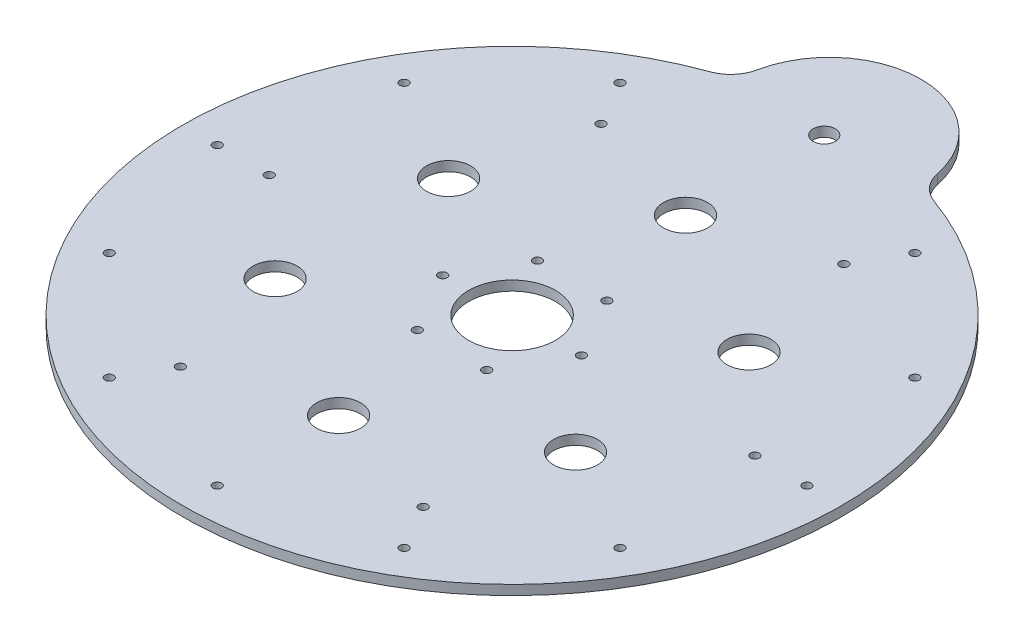
SolidWorks part; units mm, degrees
ref_plane "Front Plane" through (0, 0, 0) normal (0, 0, 1) x (1, 0, 0)
ref_plane "Top Plane" through (0, 0, 0) normal (0, 1, 0) x (1, 0, 0)
ref_plane "Right Plane" through (0, 0, 0) normal (1, 0, 0) x (0, 0, -1)
sketch "Sketch1" plane through (0, 0, 0) normal (0, -1, 0) x (1, 0, 0)
  line L0 (0, 0) -> (0, -337.6782) construction
  arc A0 (-51.8173, -193.4909) -> (51.8173, -193.4909) centre (0, -182.9328) ccw
  circle A1 centre (0, 0) radius 25
  circle A2 centre (0, 100) radius 12.7
  arc A3 (-51.8173, -193.4909) -> (-64.6132, -178.676) centre (-71.4146, -197.484) ccw
  arc A4 (51.8173, -193.4909) -> (64.6132, -178.676) centre (71.4146, -197.484) cw
  arc A5 (64.6132, -178.676) -> (-64.6132, -178.676) centre (0, 0) ccw
  circle A9 centre (-0.0097, -180) radius 6.35
  point P0 (0, 0)
  dimension "D1" = 20
  dimension "D2" = 50
  dimension "D3" = 20
extrude "Boss-Extrude1" add sketch "Sketch1" along normal blind 5.6
hole_wizard "Ø5.0mm Dowel Hole2" positions "Sketch7" profile "Sketch6" hole size "Ø5.0" standard "ANSI Metric" end condition through all
sketch "Sketch7" plane through (0, 0, 0) normal (0, -1, 0) x (1, 0, 0)
  point P0 (-147.2243, -85)
sketch "Sketch6" plane through (-147.2243, 0, -85) normal (1, 0, 0) x (0, 0, 1)
  line L0 (0, 0) -> (0, 5.6)
  line L1 (0, 5.6) -> (2.5, 5.6)
  line L2 (2.5, 5.6) -> (2.5, 0)
  line L5 (2.5, 0) -> (0, 0)
  line L11 (0, -6.35) -> (0, 107.95) construction
  dimension "Thru Hole Dia." = 5
  dimension "Thru Hole Depth" = 5.6
hole_wizard "Ø5.0mm Dowel Hole3" positions "Sketch9" profile "Sketch8" hole size "Ø5.0" standard "ANSI Metric" end condition through all
sketch "Sketch9" plane through (0, 0, 0) normal (0, 1, 0) x (1, 0, 0)
  point P0 (-170, 0)
  point P3 (-140, 0)
  point P6 (-147.2243, 85)
  point P9 (-70, 121.2436)
  point P12 (-85, 147.2243)
  point P18 (85, 147.2243)
  point P21 (70, 121.2436)
  point P24 (147.2243, 85)
  point P27 (140, 0)
  point P30 (170, 0)
  point P33 (147.2243, -85)
  point P36 (70, -121.2436)
  point P39 (85, -147.2243)
  point P45 (-85, -147.2243)
  point P48 (-70, -121.2436)
  point P51 (-20, -34.641)
  point P54 (20, -34.641)
  point P57 (40, 0)
  point P60 (-40, 0)
  point P63 (-20, 34.641)
  point P66 (20, 34.641)
  point P69 (-147.2243, -85)
  point P75 (0, -170)
sketch "Sketch8" plane through (-170, 0, 0) normal (1, 0, 0) x (0, 0, 1)
  line L0 (0, 0) -> (0, 5.6)
  line L1 (0, 5.6) -> (2.5, 5.6)
  line L2 (2.5, 5.6) -> (2.5, 0)
  line L5 (2.5, 0) -> (0, 0)
  line L11 (0, -6.35) -> (0, 107.95) construction
  dimension "Thru Hole Dia." = 5
  dimension "Thru Hole Depth" = 5.6
sketch "Sketch10" plane through (0, 0, 0) normal (0, 1, 0) x (-1, 0, 0)
  circle A0 centre (0, 100) radius 12.7
  circle A1 centre (86.6025, 50) radius 12.7
  circle A2 centre (86.6025, -50) radius 12.7
  circle A3 centre (0, -100) radius 12.7
  circle A4 centre (-86.6025, -50) radius 12.7
  circle A5 centre (-86.6025, 50) radius 12.7
  point P16 (0, 0)
  dimension "D1" = 6
extrude "Cut-Extrude1" cut sketch "Sketch10" against normal blind 20
